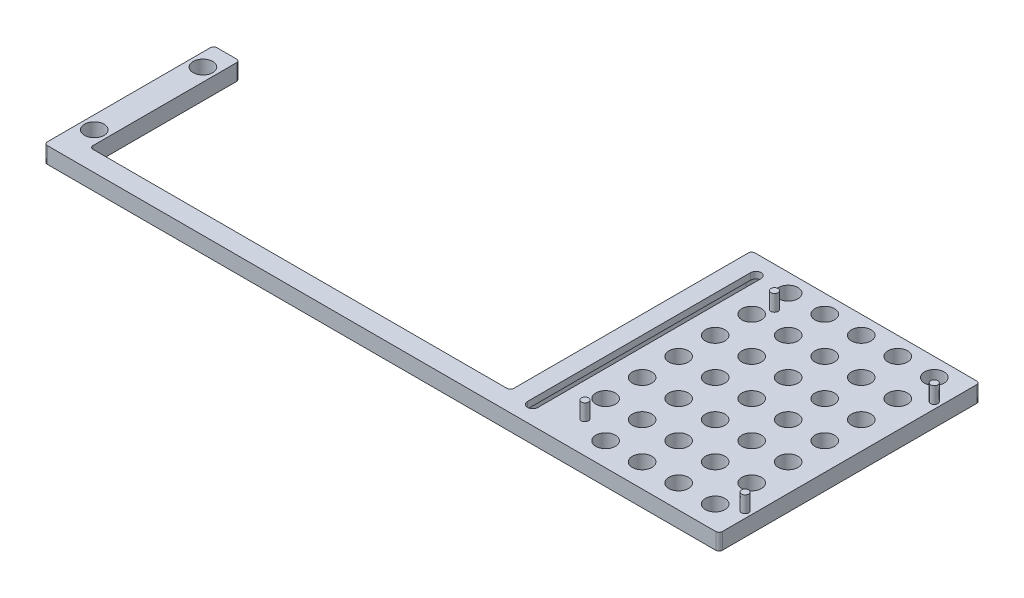
SolidWorks part; units mm, degrees
ref_plane "Front Plane" through (0, 0, 0) normal (0, 0, 1) x (1, 0, 0)
ref_plane "Top Plane" through (0, 0, 0) normal (0, 1, 0) x (1, 0, 0)
ref_plane "Right Plane" through (0, 0, 0) normal (1, 0, 0) x (0, 0, -1)
sketch "Sketch1" plane through (0, 0, 0) normal (0, 1, 0) x (1, 0, 0)
  line L0 (-27.8194, 34.0968) -> (-27.8194, -34.3032) construction
  line L1 (-35, 40) -> (35, 40)
  line L2 (-35, 40) -> (-35, -34)
  line L3 (-35, -40) -> (35, -40)
  line L4 (35, 40) -> (35, -40)
  line L5 (-35, 40) -> (35, -40) construction
  line L6 (-35, -40) -> (35, 40) construction
  line L7 (-35, -40) -> (-172, -40)
  line L9 (-35, -34) -> (-164, -34)
  line L10 (-172, -40) -> (-172, -34)
  line L11 (-26.2194, 34.0968) -> (-26.2194, -34.3032)
  line L12 (-29.4194, 34.0968) -> (-29.4194, -34.3032)
  line L15 (-172, -34) -> (-172, 12)
  line L16 (-172, 12) -> (-164, 12)
  line L17 (-164, -34) -> (-164, 12)
  circle A59 centre (-18.2, 34.4) radius 3
  circle A60 centre (-7, 34.4) radius 3
  circle A61 centre (4.2, 34.4) radius 3
  circle A62 centre (15.4, 34.4) radius 3
  circle A63 centre (26.6, 34.4) radius 3
  circle A64 centre (-18.2, 23.2) radius 3
  circle A65 centre (-7, 23.2) radius 3
  circle A66 centre (4.2, 23.2) radius 3
  circle A67 centre (15.4, 23.2) radius 3
  circle A68 centre (26.6, 23.2) radius 3
  circle A69 centre (-18.2, 12) radius 3
  circle A70 centre (-7, 12) radius 3
  circle A71 centre (4.2, 12) radius 3
  circle A72 centre (15.4, 12) radius 3
  circle A73 centre (26.6, 12) radius 3
  circle A74 centre (-18.2, 0.8) radius 3
  circle A75 centre (-7, 0.8) radius 3
  circle A76 centre (4.2, 0.8) radius 3
  circle A77 centre (15.4, 0.8) radius 3
  circle A78 centre (26.6, 0.8) radius 3
  circle A79 centre (-18.2, -10.4) radius 3
  circle A80 centre (-7, -10.4) radius 3
  circle A81 centre (4.2, -10.4) radius 3
  circle A82 centre (15.4, -10.4) radius 3
  circle A83 centre (26.6, -10.4) radius 3
  circle A84 centre (-18.2, -21.6) radius 3
  circle A85 centre (-7, -21.6) radius 3
  circle A86 centre (4.2, -21.6) radius 3
  circle A87 centre (15.4, -21.6) radius 3
  circle A88 centre (26.6, -21.6) radius 3
  circle A90 centre (-7, -32.8) radius 3
  circle A91 centre (4.2, -32.8) radius 3
  circle A92 centre (15.4, -32.8) radius 3
  circle A93 centre (26.6, -32.8) radius 3
  circle A100 centre (-168, 4.7188) radius 3
  circle A101 centre (-168, -28.6042) radius 3
  arc A103 (-26.2194, 34.0968) -> (-29.4194, 34.0968) centre (-27.8194, 34.0968) ccw
  arc A104 (-29.4194, -34.3032) -> (-26.2194, -34.3032) centre (-27.8194, -34.3032) ccw
  point P9 (-27.8194, -0.1032)
  dimension "D5" = 8
  dimension "D6" = 4
  dimension "D1" = 70
  dimension "D2" = 80
  dimension "D3" = 137
  dimension "D4" = 6
  dimension "D7" = 4
extrude "Boss-Extrude2" add sketch "Sketch1" along normal blind 5
sketch "Sketch2" plane through (0, 5, 0) normal (0, 1, 0) x (1, 0, 0)
  line L0 (35, -40) -> (35, 40) construction
  line L1 (-172, -40) -> (35, -40) construction
  circle A0 centre (33, -30) radius 1.1
  circle A1 centre (-15.9998, -30.1245) radius 1.1
  circle A2 centre (-15.9998, 28) radius 1.1
  circle A3 centre (33, 28) radius 1.1
  point P8 (0, 0)
  point P13 (0, 0)
  point P14 (0, 0)
  point P15 (33, 28)
  point P16 (0, 0)
  point P17 (-15.9998, 28)
  dimension "D1" = 49
  dimension "D2" = 2
  dimension "D3" = 10
  dimension "D4" = 58
extrude "Boss-Extrude3" add sketch "Sketch2" along normal blind 5
fillet "Fillet1" radius 1 8 edges at (-172, 2.5, 40) (-172, 2.5, -12) (-164, 2.5, -12) (-164, 2.5, 34) (-35, 2.5, 34) (-35, 2.5, -40) (35, 2.5, -40) (35, 2.5, 40)
sketch "Sketch5" plane through (0, 0, 0) normal (0, -1, 0) x (1, 0, 0)
  line L0 (-27.8194, 34.3032) -> (-27.8194, -33.8415) construction
  line L1 (-25.0694, 34.3032) -> (-25.0694, -33.8415)
  line L2 (-30.5694, 34.3032) -> (-30.5694, -33.8415)
  arc A0 (-25.0694, 34.3032) -> (-30.5694, 34.3032) centre (-27.8194, 34.3032) ccw
  arc A1 (-30.5694, -33.8415) -> (-25.0694, -33.8415) centre (-27.8194, -33.8415) ccw
  point P3 (-27.8194, 0.2309)
extrude "Cut-Extrude1" cut sketch "Sketch5" against normal blind 3
